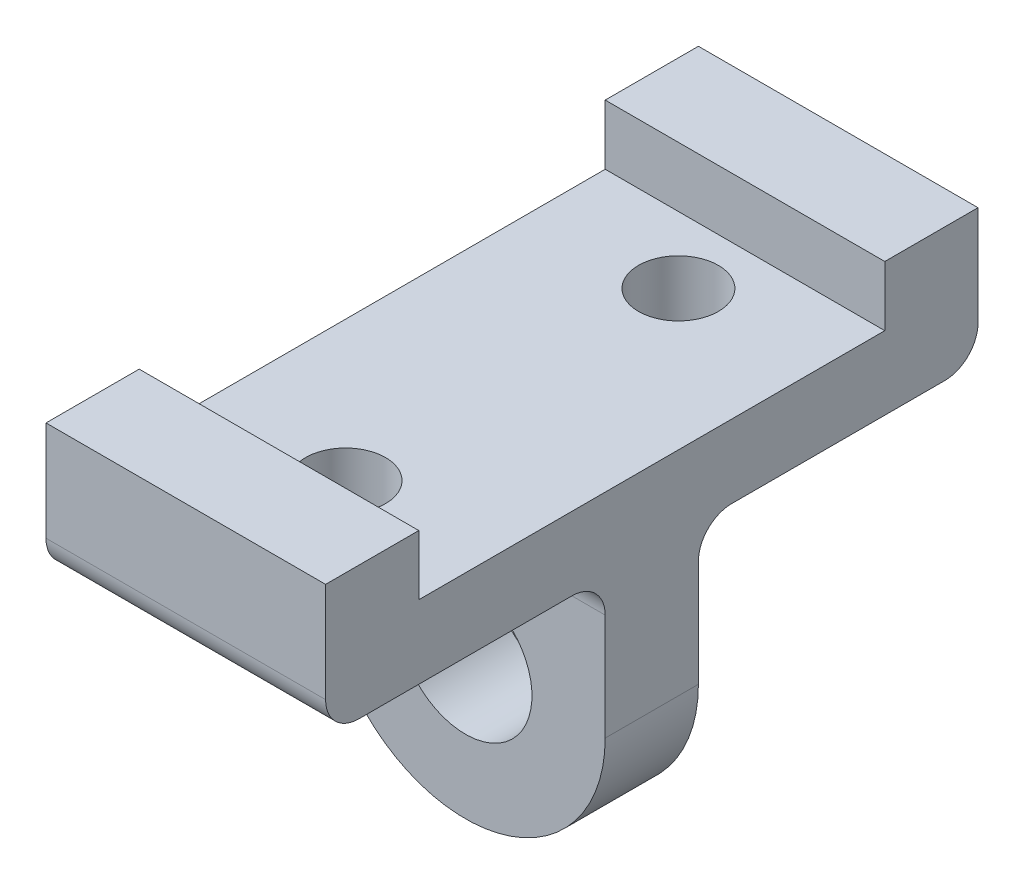
SolidWorks part; units mm, degrees
ref_plane "Alzado" through (0, 0, 0) normal (0, 0, 1) x (1, 0, 0)
ref_plane "Planta" through (0, 0, 0) normal (0, 1, 0) x (1, 0, 0)
ref_plane "Vista lateral" through (0, 0, 0) normal (1, 0, 0) x (0, 0, -1)
sketch "Sketch1" plane through (0, 0, 0) normal (0, 1, 0) x (1, 0, 0)
  line L1 (-21, -49) -> (21, -49)
  line L2 (-21, -49) -> (-21, 49)
  line L3 (-21, 49) -> (21, 49)
  line L4 (21, -49) -> (21, 49)
  line L5 (-21, -49) -> (21, 49) construction
  line L6 (-21, 49) -> (21, -49) construction
  point P0 (0, 0)
  dimension "D1" = 42
  dimension "D2" = 98
extrude "Boss-Extrude1" add sketch "Sketch1" along normal blind 20
sketch "Sketch2" plane through (0, 20, 0) normal (0, 1, 0) x (1, 0, 0)
  line L5 (21, -49) -> (21, -35)
  line L6 (21, -49) -> (21, 49) construction
  line L7 (21, 49) -> (21, 35)
  line L8 (-21, 49) -> (-21, -49) construction
  line L9 (21, -35) -> (-21, -35)
  line L10 (21, -35) -> (21, 35)
  line L11 (21, 35) -> (-21, 35)
  line L12 (-21, -35) -> (-21, 35)
  line M7 (21, -49) -> (21, 49)
  line M9 (-21, 49) -> (-21, -49)
  dimension "D1" = 70
extrude "Cut-Extrude1" cut sketch "Sketch2" against normal blind 9 contours L11 L9 M7 M9
sketch "Sketch3" plane through (0, 0, 0) normal (0, -1, 0) x (1, 0, 0)
  line L0 (-21, 0) -> (21, 0) construction
  line L3 (-21, -49) -> (-21, 49) construction
  line L4 (21, 49) -> (21, -49) construction
  circle A0 centre (0, -25) radius 6
  circle A1 centre (0, 25) radius 6
sketch "Sketch4" plane through (0, 0, 0) normal (0, -1, 0) x (1, 0, 0)
  line L1 (-21, -49) -> (-21, 49) construction
  line L2 (21, 49) -> (21, -49) construction
  line L3 (-21, -7) -> (21, -7)
  line L4 (-21, -7) -> (-21, 7)
  line L5 (-21, 7) -> (21, 7)
  line L6 (21, -7) -> (21, 7)
  dimension "D1" = 14
extrude "Boss-Extrude2" add sketch "Sketch4" along normal blind 21
sketch "Sketch5" plane through (0, -21, 0) normal (0, -1, 0) x (1, 0, 0)
  line L0 (-21, -7) -> (21, -7) construction
  line L1 (21, 7) -> (0, 7)
  line L2 (21, 7) -> (21, -7)
  line L3 (21, -7) -> (0, -7)
  line L4 (0, 7) -> (0, -7)
revolve "Revolve1" add sketch "Sketch5" angle 180 about L4
extrude "Cut-Extrude2" cut sketch "Sketch3" against normal blind 21
sketch "Sketch6" plane through (0, 0, -7) normal (0, 0, -1) x (-1, 0, 0)
  line L0 (0, 0) -> (0, -21) construction
  line L1 (21, 0) -> (-21, 0) construction
  circle A0 centre (0, -21) radius 10
extrude "Cut-Extrude3" cut sketch "Sketch6" against normal blind 21
fillet "Fillet1" radius 5 4 edges at (0, 0, 49) (0, 0, -49) (0, 0, -7) (0, 0, 7)
